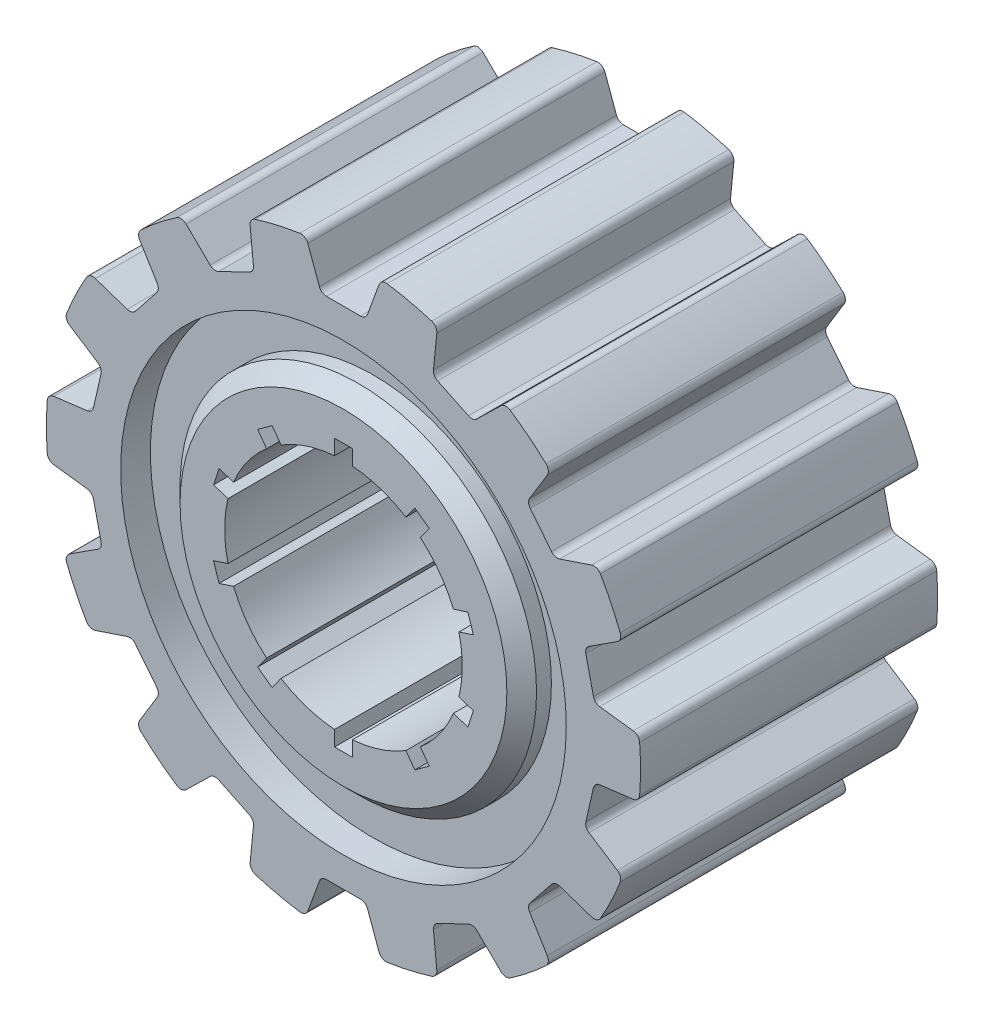
SolidWorks part; units mm, degrees
ref_plane "Front Plane" through (0, 0, 0) normal (0, 0, 1) x (1, 0, 0)
ref_plane "Top Plane" through (0, 0, 0) normal (0, 1, 0) x (1, 0, 0)
ref_plane "Right Plane" through (0, 0, 0) normal (1, 0, 0) x (0, 0, -1)
sketch "Sketch1" plane through (0, 0, 0) normal (0, 0, 1) x (1, 0, 0)
  line L0 (0, 0) -> (0, 5.5132) construction
  line L1 (2.8877, 3.4642) -> (2.4023, 3.8169)
  line L3 (0.3, 3.9887) -> (0.3, 4.5)
  line L4 (0.3, 4.5) -> (-0.3, 4.5)
  line L5 (-0.3, 3.9887) -> (-0.3, 4.5)
  line L6 (0, 4) -> (-0.3, 4.5) construction
  line L7 (0.3, 4.5) -> (0, 4) construction
  line L8 (2.5872, 3.0506) -> (2.8877, 3.4642)
  line L9 (2.1018, 3.4033) -> (2.4023, 3.8169)
  line L10 (4.3725, 1.1053) -> (4.187, 1.6759)
  line L11 (3.8862, 0.9473) -> (4.3725, 1.1053)
  line L12 (3.7008, 1.5179) -> (4.187, 1.6759)
  line L13 (4.187, -1.6759) -> (4.3725, -1.1053)
  line L14 (3.7008, -1.5179) -> (4.187, -1.6759)
  line L15 (3.8862, -0.9473) -> (4.3725, -1.1053)
  line L16 (2.4023, -3.8169) -> (2.8877, -3.4642)
  line L17 (2.1018, -3.4033) -> (2.4023, -3.8169)
  line L18 (2.5872, -3.0506) -> (2.8877, -3.4642)
  line L19 (-0.3, -4.5) -> (0.3, -4.5)
  line L20 (-0.3, -3.9887) -> (-0.3, -4.5)
  line L21 (0.3, -3.9887) -> (0.3, -4.5)
  line L22 (-2.8877, -3.4642) -> (-2.4023, -3.8169)
  line L23 (-2.5872, -3.0506) -> (-2.8877, -3.4642)
  line L24 (-2.1018, -3.4033) -> (-2.4023, -3.8169)
  line L25 (-4.3725, -1.1053) -> (-4.187, -1.6759)
  line L26 (-3.8862, -0.9473) -> (-4.3725, -1.1053)
  line L27 (-3.7008, -1.5179) -> (-4.187, -1.6759)
  line L28 (-4.187, 1.6759) -> (-4.3725, 1.1053)
  line L29 (-3.7008, 1.5179) -> (-4.187, 1.6759)
  line L30 (-3.8862, 0.9473) -> (-4.3725, 1.1053)
  line L31 (-2.4023, 3.8169) -> (-2.8877, 3.4642)
  line L32 (-2.1018, 3.4033) -> (-2.4023, 3.8169)
  line L33 (-2.5872, 3.0506) -> (-2.8877, 3.4642)
  circle A0 centre (0, 0) radius 10
  arc A1 (-0.3, 3.9887) -> (-2.1018, 3.4033) centre (0, 0) ccw
  arc A2 (-3.8862, 0.9473) -> (-3.8862, -0.9473) centre (0, 0) ccw
  arc A3 (-2.5872, 3.0506) -> (-3.7008, 1.5179) centre (0, 0) ccw
  arc A4 (-3.7008, -1.5179) -> (-2.5872, -3.0506) centre (0, 0) ccw
  arc A5 (-2.1018, -3.4033) -> (-0.3, -3.9887) centre (0, 0) ccw
  arc A6 (0.3, -3.9887) -> (2.1018, -3.4033) centre (0, 0) ccw
  arc A7 (2.5872, -3.0506) -> (3.7008, -1.5179) centre (0, 0) ccw
  arc A8 (3.8862, -0.9473) -> (3.8862, 0.9473) centre (0, 0) ccw
  arc A9 (3.7008, 1.5179) -> (2.5872, 3.0506) centre (0, 0) ccw
  arc A10 (2.1018, 3.4033) -> (0.3, 3.9887) centre (0, 0) ccw
  point P5 (0, 4.5)
  point P6 (0, 4)
  point P50 (0, 0)
  dimension "D1" = 20
  dimension "D2" = 8
  dimension "D3" = 0.6
  dimension "D4" = 4.5
  dimension "D5" = 10
extrude "Boss-Extrude1" add sketch "Sketch1" along normal blind 10
sketch "Sketch2" plane through (0, 0, 10) normal (0, 0, 1) x (1, 0, 0)
  line L0 (0, 0) -> (0, 10) construction
  line L1 (-0.75, 8.5) -> (0.75, 8.5)
  line L2 (0.75, 8.5) -> (1.2666, 9.9195)
  line L3 (-0.75, 8.5) -> (-1.2666, 9.9195)
  circle A0 centre (0, 0) radius 10 construction
  point P8 (0, 0)
  point P11 (0, 0)
  point P12 (0, 0)
  point P13 (0, 0)
  point P14 (0, 0)
  circle M5 centre (0, 0) radius 10
  dimension "D1" = 1.5
  dimension "D2" = 0.75
  dimension "D3" = 110
  dimension "D4" = 110
  dimension "D5" = 8.5
extrude "Cut-Extrude1" cut sketch "Sketch2" against normal through all and the other way through all contours L1 L0 L3 M5 | L0 L1 L2 M5
pattern_circular "CirPattern1" count 14 over 360 about axis through (0, 0, 0) along (0, 0, 1) of "Cut-Extrude1"
ref_plane "Plane1" through (0, 0, 5) normal (0, 0, 1) x (1, 0, 0)
sketch "Sketch3" plane through (0, 0, 5) normal (0, 0, 1) x (1, 0, 0)
  circle A0 centre (0, 0) radius 7.5
  circle A1 centre (0, 0) radius 6
  dimension "D1" = 15
  dimension "D2" = 12
extrude "Cut-Extrude2" cut sketch "Sketch3" against normal through all from offset 4 offset against normal yes
chamfer "Chamfer1" distance 0.5 angle 45 1 edges at (6, 0, 0)
mirror "Mirror2" about plane through (0, 0, 5) normal (0, 0, 1) of "Cut-Extrude2"
chamfer "Chamfer2" distance 0.5 angle 45 1 edges at (6, 0, 10)
fillet "Fillet1" radius 0.25 56 edges at (-8.12, 2.6226, 5) (-8.4538, 1.1602, 5) (-8.4538, -1.1602, 5) (-8.12, -2.6226, 5) (-7.1132, -4.7133, 5) (-6.178, -5.886, 5) (-4.3637, -7.3328, 5) (-3.0123, -7.9836, 5) (-0.75, -8.5, 5) (0.75, -8.5, 5) (3.0123, -7.9836, 5) (4.3637, -7.3328, 5) (6.178, -5.886, 5) (7.1132, -4.7133, 5) (8.12, -2.6226, 5) (8.4538, -1.1602, 5) (8.4538, 1.1602, 5) (8.12, 2.6226, 5) (7.1132, 4.7133, 5) (6.178, 5.886, 5) (4.3637, 7.3328, 5) (3.0123, 7.9836, 5) (0.75, 8.5, 5) (-0.75, 8.5, 5) (-3.0123, 7.9836, 5) (-4.3637, 7.3328, 5) (-6.178, 5.886, 5) (-7.1132, 4.7133, 5)
